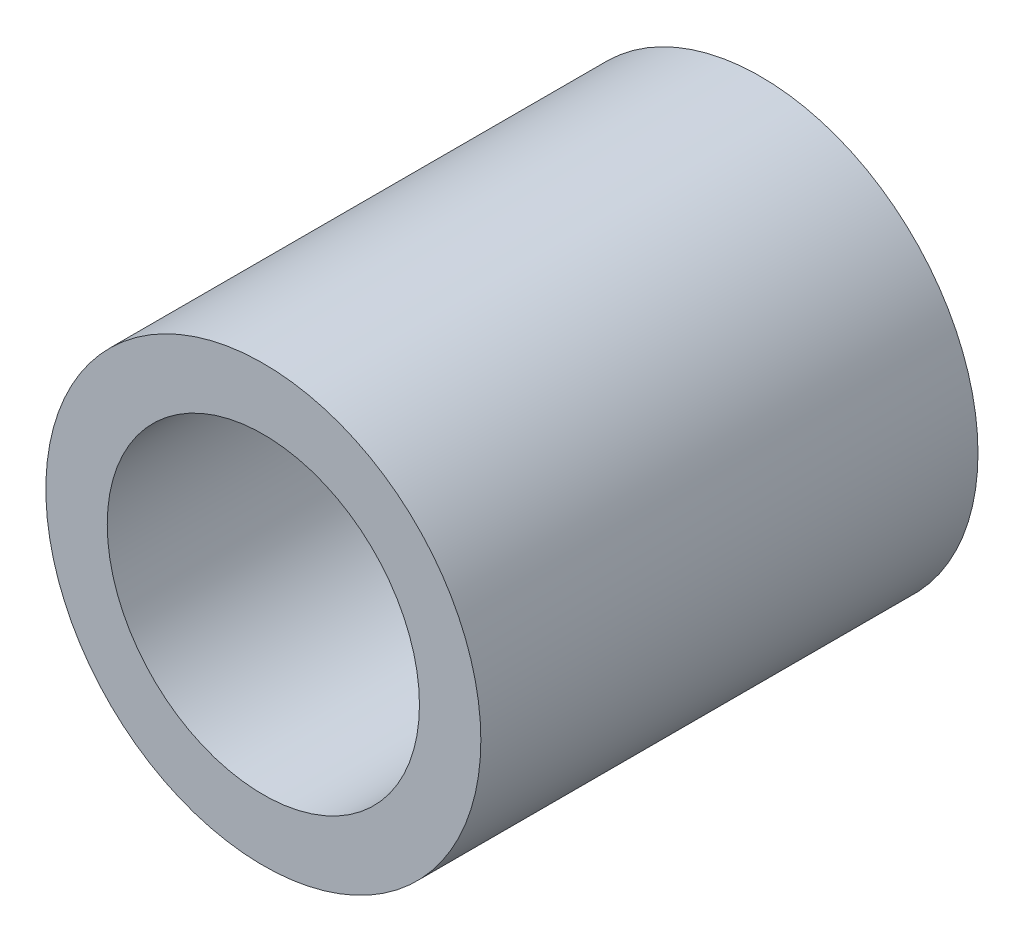
SolidWorks part; units mm, degrees
ref_plane "Front Plane" through (0, 0, 0) normal (0, 0, 1) x (1, 0, 0)
ref_plane "Top Plane" through (0, 0, 0) normal (0, 1, 0) x (1, 0, 0)
ref_plane "Right Plane" through (0, 0, 0) normal (1, 0, 0) x (0, 0, -1)
sketch "Sketch1" plane through (0, 0, 0) normal (0, 0, 1) x (1, 0, 0)
  circle A0 centre (0, 0) radius 5.5562
  circle A1 centre (0, 0) radius 3.9878
  dimension "D1" = 11.1125
  dimension "ID" = 7.9756
extrude "Extrude1" add sketch "Sketch1" along normal mid plane 12.7
sketch "Sketch2" plane through (0, 0, 0) normal (1, 0, 0) x (0, 0, -1)
  line L0 (-6.35, -3.9878) -> (6.35, -3.9878) construction
  line L3 (6.35, 3.9878) -> (-6.35, 3.9878) construction
  line L5 (-6.35, -3.9878) -> (6.35, -3.9878)
  line L6 (6.35, 3.9878) -> (-6.35, 3.9878)
sketch "Sketch4" plane through (0, 0, 6.35) normal (0, 0, 1) x (1, 0, 0)
  line L0 (0, 0) -> (-2.8198, 2.8198)
  line L1 (0, -6.985) -> (0, 6.985) construction
  circle A0 centre (0, 0) radius 3.9878 construction
  dimension "D1" = 45
